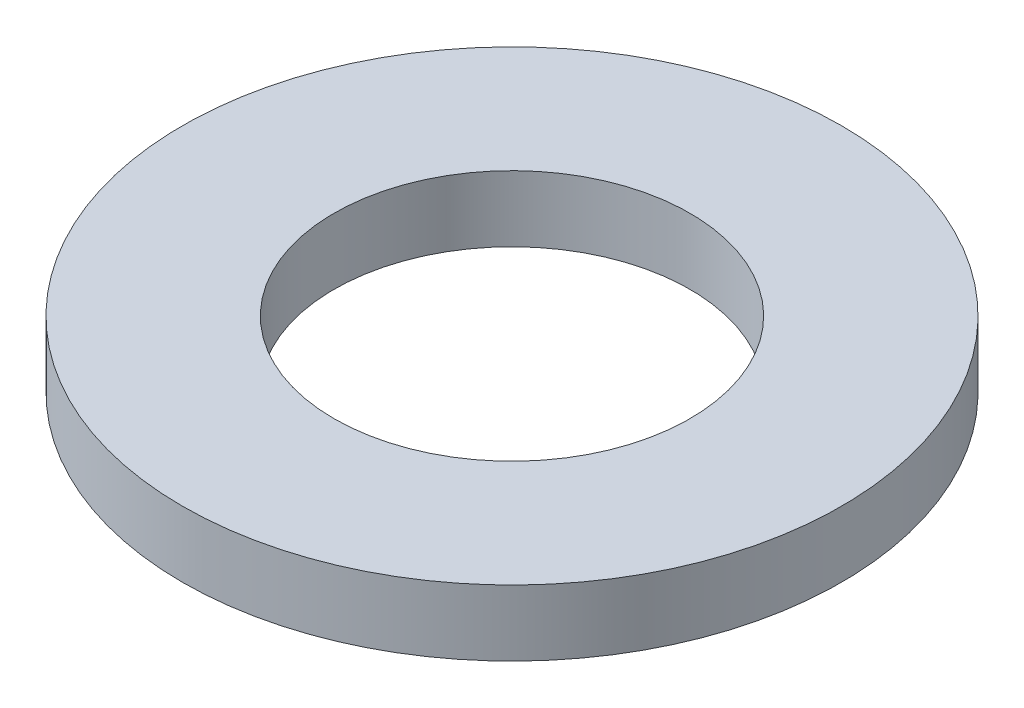
SolidWorks part; units mm, degrees
material "1.4057 (X17CrNi16-2)"
ref_plane "Plano frontal" through (0, 0, 0) normal (0, 0, 1) x (1, 0, 0)
ref_plane "Plano superior" through (0, 0, 0) normal (0, 1, 0) x (1, 0, 0)
ref_plane "Plano direito" through (0, 0, 0) normal (1, 0, 0) x (0, 0, -1)
sketch "Esboço1" plane through (0, 0, 0) normal (0, 1, 0) x (1, 0, 0)
  circle A0 centre (0, 0) radius 5
  circle A1 centre (0, 0) radius 2.7
  dimension "D1" = 5.4
  dimension "D2" = 10
extrude "Ressalto-extrusão1" add sketch "Esboço1" along normal blind 1
